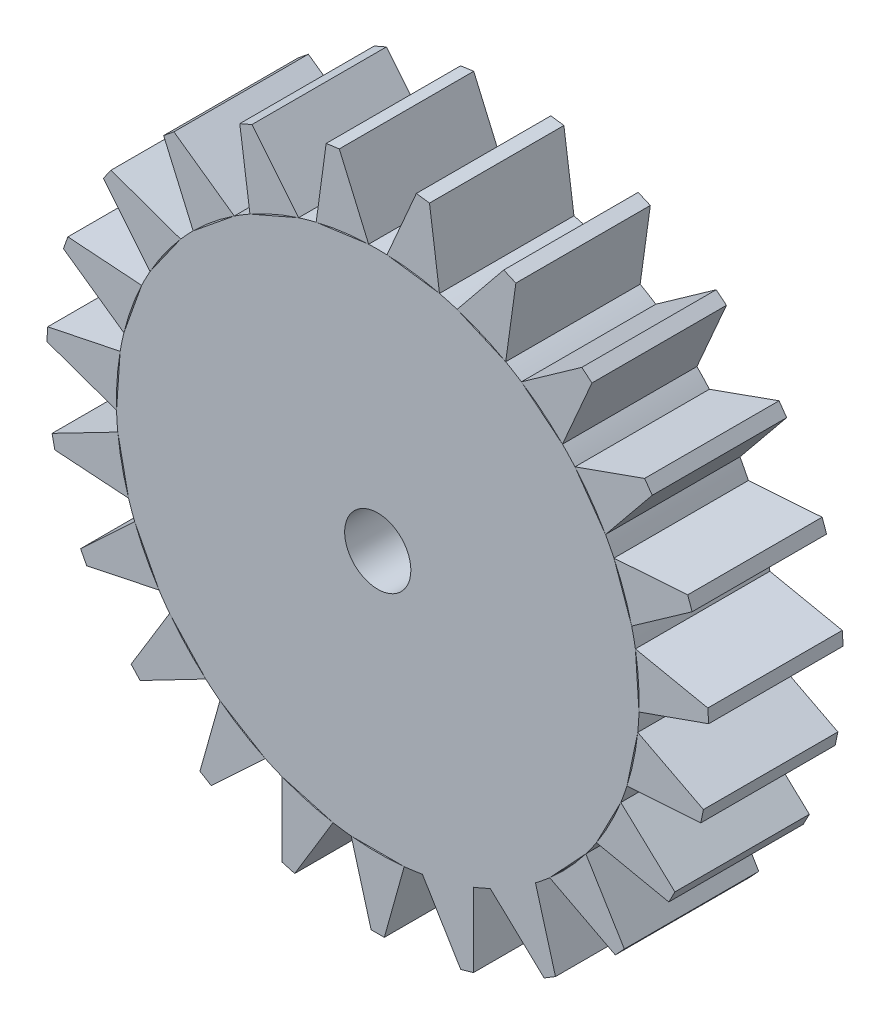
SolidWorks part; units mm, degrees
ref_plane "Front Plane" through (0, 0, 0) normal (0, 0, 1) x (1, 0, 0)
ref_plane "Top Plane" through (0, 0, 0) normal (0, 1, 0) x (1, 0, 0)
ref_plane "Right Plane" through (0, 0, 0) normal (1, 0, 0) x (0, 0, -1)
sketch "Sketch2" plane through (0, 0, 0) normal (0, 0, 1) x (1, 0, 0)
  circle A0 centre (0, 0) radius 25.15
  dimension "D1" = 50.3
sketch "Sketch1" plane through (0, 0, 0) normal (0, 0, 1) x (1, 0, 0)
  line L0 (-0.5041, -25.0311) -> (0.4959, -25.0311)
  line L1 (0.4959, -25.0311) -> (1.9977, -19.6487)
  line L2 (-7.2387, -23.9669) -> (-7.2327, -18.3789)
  line L3 (-0.5041, -25.0311) -> (-2.0059, -19.6487)
  line L4 (-6.2758, -24.2367) -> (-3.3776, -19.459)
  line L5 (-7.2387, -23.9669) -> (-6.2758, -24.2367)
  line L6 (-13.4365, -21.1252) -> (-11.923, -15.746)
  line L7 (-12.5821, -21.6447) -> (-8.5023, -17.8262)
  line L8 (-13.4365, -21.1252) -> (-12.5821, -21.6447)
  line L9 (-18.6377, -16.7167) -> (-15.7291, -11.9453)
  line L10 (-17.9552, -17.4475) -> (-12.9965, -14.8713)
  line L11 (-18.6377, -16.7167) -> (-17.9552, -17.4475)
  line L12 (-22.4567, -11.0684) -> (-18.3686, -7.2587)
  line L13 (-21.9966, -11.9562) -> (-16.5267, -10.8134)
  line L14 (-22.4567, -11.0684) -> (-21.9966, -11.9562)
  line L15 (-24.6101, -4.5992) -> (-19.6458, -2.0337)
  line L16 (-24.4067, -5.5783) -> (-18.8313, -5.9535)
  line L17 (-24.6101, -4.5992) -> (-24.4067, -5.5783)
  line L18 (-24.9384, 2.2111) -> (-19.466, 3.3421)
  line L19 (-25.0066, 1.2134) -> (-19.7392, -0.6521)
  line L20 (-24.9384, 2.2111) -> (-25.0066, 1.2134)
  line L21 (-23.417, 8.8574) -> (-17.8425, 8.47)
  line L22 (-23.7519, 7.9152) -> (-19.1832, 4.6976)
  line L23 (-23.417, 8.8574) -> (-23.7519, 7.9152)
  line L24 (-20.159, 14.8468) -> (-14.8956, 12.9698)
  line L25 (-20.7356, 14.0298) -> (-17.2044, 9.699)
  line L26 (-20.159, 14.8468) -> (-20.7356, 14.0298)
  line L27 (-15.4058, 19.7351) -> (-10.8441, 16.5076)
  line L28 (-16.1815, 19.104) -> (-13.9497, 13.981)
  line L29 (-15.4058, 19.7351) -> (-16.1815, 19.104)
  line L30 (-9.5101, 23.1597) -> (-5.9882, 18.8212)
  line L31 (-10.4273, 22.7613) -> (-9.6604, 17.2261)
  line L32 (-9.5101, 23.1597) -> (-10.4273, 22.7613)
  line L33 (-2.909, 24.8666) -> (-0.6883, 19.7388)
  line L34 (-3.8997, 24.7305) -> (-4.6546, 19.1937)
  line L35 (-2.909, 24.8666) -> (-3.8997, 24.7305)
  line L36 (3.9078, 24.7293) -> (4.6627, 19.1926)
  line L37 (2.9171, 24.8655) -> (0.6964, 19.7377)
  line L38 (3.9078, 24.7293) -> (2.9171, 24.8655)
  line L39 (10.4348, 22.758) -> (9.6679, 17.2229)
  line L40 (9.5176, 23.1564) -> (5.9958, 18.8179)
  line L41 (10.4348, 22.758) -> (9.5176, 23.1564)
  line L42 (16.1879, 19.0988) -> (13.9561, 13.9758)
  line L43 (15.4122, 19.7299) -> (10.8504, 16.5024)
  line L44 (16.1879, 19.0988) -> (15.4122, 19.7299)
  line L45 (20.7404, 14.0231) -> (17.2092, 9.6923)
  line L46 (20.1637, 14.8401) -> (14.9004, 12.9631)
  line L47 (20.7404, 14.0231) -> (20.1637, 14.8401)
  line L48 (23.7547, 7.9074) -> (19.1859, 4.6899)
  line L49 (23.4198, 8.8497) -> (17.8452, 8.4623)
  line L50 (23.7547, 7.9074) -> (23.4198, 8.8497)
  line L51 (25.0072, 1.2053) -> (19.7398, -0.6603)
  line L52 (24.9389, 2.2029) -> (19.4666, 3.3339)
  line L53 (25.0072, 1.2053) -> (24.9389, 2.2029)
  line L54 (24.405, -5.5863) -> (18.8296, -5.9616)
  line L55 (24.6085, -4.6072) -> (19.6442, -2.0418)
  line L56 (24.405, -5.5863) -> (24.6085, -4.6072)
  line L57 (21.9928, -11.9635) -> (16.523, -10.8207)
  line L58 (22.4529, -11.0756) -> (18.3649, -7.266)
  line L59 (21.9928, -11.9635) -> (22.4529, -11.0756)
  line L60 (17.9496, -17.4535) -> (12.9909, -14.8773)
  line L61 (18.6321, -16.7227) -> (15.7235, -11.9513)
  line L62 (17.9496, -17.4535) -> (18.6321, -16.7227)
  line L63 (12.5751, -21.649) -> (8.4953, -17.8305)
  line L64 (13.4295, -21.1294) -> (11.916, -15.7503)
  line L65 (12.5751, -21.649) -> (13.4295, -21.1294)
  line L66 (6.2679, -24.2389) -> (3.3697, -19.4613)
  line L67 (7.2308, -23.9691) -> (7.2248, -18.3811)
  line L68 (6.2679, -24.2389) -> (7.2308, -23.9691)
  line L69 (-19.7392, -0.6521) -> (-19.466, 3.3421)
  line L70 (-2.0059, -19.6487) -> (1.9977, -19.6487)
  line L71 (-7.2327, -18.3789) -> (-3.3776, -19.459)
  line L72 (-11.923, -15.746) -> (-8.5023, -17.8262)
  line L73 (-15.7291, -11.9453) -> (-12.9965, -14.8713)
  line L74 (-18.3686, -7.2587) -> (-16.5267, -10.8134)
  line L75 (-19.6458, -2.0337) -> (-18.8313, -5.9535)
  line L76 (-19.466, 3.3421) -> (-19.7392, -0.6521)
  line L77 (-17.8425, 8.47) -> (-19.1832, 4.6976)
  line L78 (-14.8956, 12.9698) -> (-17.2044, 9.699)
  line L79 (-10.8441, 16.5076) -> (-13.9497, 13.981)
  line L80 (-5.9882, 18.8212) -> (-9.6604, 17.2261)
  line L81 (-0.6883, 19.7388) -> (-4.6546, 19.1937)
  line L82 (4.6627, 19.1926) -> (0.6964, 19.7377)
  line L83 (9.6679, 17.2229) -> (5.9958, 18.8179)
  line L84 (13.9561, 13.9758) -> (10.8504, 16.5024)
  line L85 (17.2092, 9.6923) -> (14.9004, 12.9631)
  line L86 (19.1859, 4.6899) -> (17.8452, 8.4623)
  line L87 (19.7398, -0.6603) -> (19.4666, 3.3339)
  line L88 (18.8296, -5.9616) -> (19.6442, -2.0418)
  line L89 (16.523, -10.8207) -> (18.3649, -7.266)
  line L90 (12.9909, -14.8773) -> (15.7235, -11.9513)
  line L91 (8.4953, -17.8305) -> (11.916, -15.7503)
  line L92 (3.3697, -19.4613) -> (7.2248, -18.3811)
  circle A0 centre (0, 0) radius 19.75
  circle A1 centre (0, 0) radius 2.5
  circle A2 centre (0, 0) radius 19.75
  point P11 (-0.0041, -25.0311)
  point P92 (0, 0)
  dimension "D1" = 39.5
  dimension "D2" = 5
  dimension "D4" = 23
  dimension "D3" = 0.5
  dimension "D5" = 105.59
  dimension "D6" = 5.588
extrude "Boss-Extrude1" add sketch "Sketch1" along normal blind 10.16 contours A0 A1 | A0 L33 L35 L34 | A0 L36 L38 L37 | A0 L39 L41 L40 | A0 L42 L44 L43 | A0 L45 L47 L46 | A0 L48 L50 L49 | A0 L51 L53 L52 | A0 L54 L56 L55 | A0 L30 L32 L31 | A0 L27 L29 L28 | A0 L24 L26 L25 | A0 L21 L23 L22 | A0 L18 L20 L19 | A0 L15 L17 L16 | A0 L12 L14 L13 | A0 L9 L11 L10 | A0 L6 L8 L7 | A0 L2 L5 L4 | A0 L3 L0 L1 | A0 L57 L59 L58 | A0 L60 L62 L61 | L63 L91 L64 L65 | L66 L92 L67 L68
